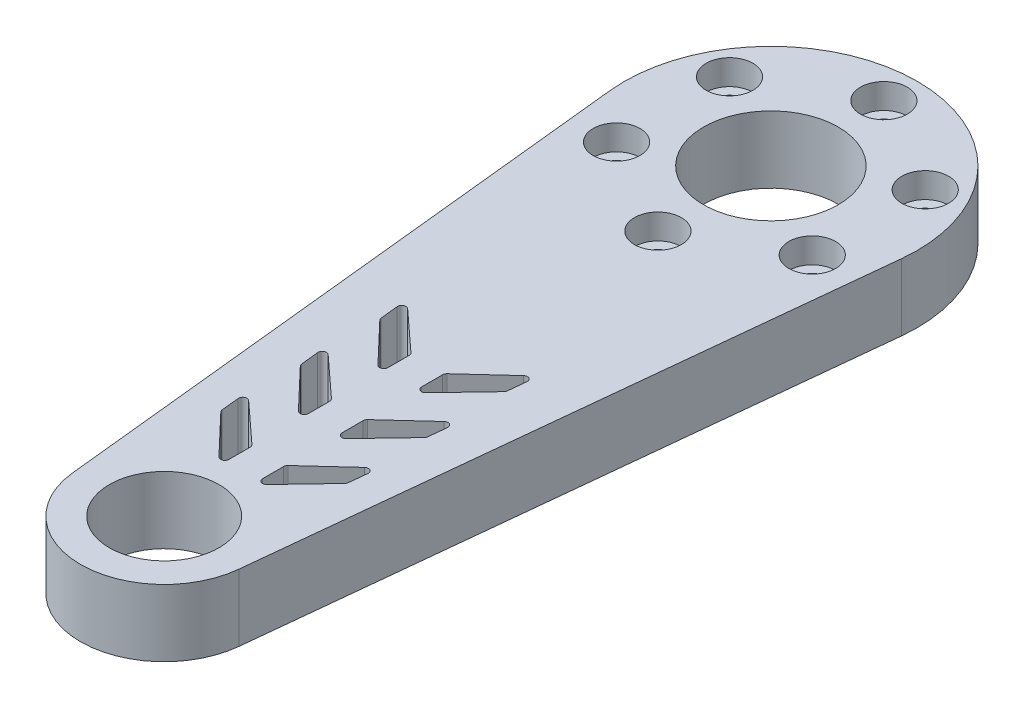
SolidWorks part; units mm, degrees
material "Thornel Mat VMA"
ref_plane "前视基准面" through (0, 0, 0) normal (0, 0, 1) x (1, 0, 0)
ref_plane "上视基准面" through (0, 0, 0) normal (0, 1, 0) x (1, 0, 0)
ref_plane "右视基准面" through (0, 0, 0) normal (1, 0, 0) x (0, 0, -1)
ref_plane "基准面4" through (0, 4, 0) normal (0, 1, 0) x (1, 0, 0)
sketch "草图1" plane through (0, 4, 0) normal (0, 1, 0) x (1, 0, 0)
  line L0 (-17.4061, -1.8103) -> (-9.9463, -73.5345)
  line L1 (9.9463, -73.5345) -> (17.4061, -1.8103)
  arc A0 (-9.9463, -73.5345) -> (9.9463, -73.5345) centre (0, -72.5) ccw
  arc A1 (17.4061, -1.8103) -> (-17.4061, -1.8103) centre (0, 0) ccw
extrude "凸台-拉伸1" add sketch "草图1" against normal blind 8
sketch "草图2" plane through (0, 4, 0) normal (0, 1, 0) x (-1, 0, 0)
  line L0 (2, 43.7505) -> (2, 41)
  line L1 (2, 41) -> (6.9232, 36.4832)
  line L2 (7.7585, 36.9034) -> (7.5188, 39.2084)
  line L3 (7.5188, 39.2084) -> (2.862, 44.0954)
  arc A0 (2.862, 44.0954) -> (2, 43.7505) centre (2.5, 43.7505) ccw
  arc A1 (6.9232, 36.4832) -> (7.7585, 36.9034) centre (7.2612, 36.8517) ccw
extrude "切除-拉伸1" cut sketch "草图2" against normal through all
sketch "草图3" plane through (0, 4, 0) normal (0, 1, 0) x (-1, 0, 0)
  line L0 (-6.9232, 36.4832) -> (-2, 41)
  line L1 (-2, 41) -> (-2, 43.7505)
  line L2 (-2.862, 44.0954) -> (-7.5188, 39.2084)
  line L3 (-7.5188, 39.2084) -> (-7.7585, 36.9034)
  arc A0 (-2, 43.7505) -> (-2.862, 44.0954) centre (-2.5, 43.7505) ccw
  arc A1 (-7.7585, 36.9034) -> (-6.9232, 36.4832) centre (-7.2612, 36.8517) ccw
extrude "切除-拉伸2" cut sketch "草图3" against normal through all
sketch "草图4" plane through (0, 4, 0) normal (0, 1, 0) x (-1, 0, 0)
  line L0 (2, 53.2505) -> (2, 50.5)
  line L1 (2, 50.5) -> (6.9232, 45.9832)
  line L2 (7.7585, 46.4034) -> (7.5188, 48.7084)
  line L3 (7.5188, 48.7084) -> (2.862, 53.5954)
  arc A0 (2.862, 53.5954) -> (2, 53.2505) centre (2.5, 53.2505) ccw
  arc A1 (6.9232, 45.9832) -> (7.7585, 46.4034) centre (7.2612, 46.3517) ccw
extrude "切除-拉伸3" cut sketch "草图4" against normal through all
sketch "草图5" plane through (0, 4, 0) normal (0, 1, 0) x (-1, 0, 0)
  line L0 (-6.9232, 45.9832) -> (-2, 50.5)
  line L1 (-2, 50.5) -> (-2, 53.2505)
  line L2 (-2.862, 53.5954) -> (-7.5188, 48.7084)
  line L3 (-7.5188, 48.7084) -> (-7.7585, 46.4034)
  arc A0 (-2, 53.2505) -> (-2.862, 53.5954) centre (-2.5, 53.2505) ccw
  arc A1 (-7.7585, 46.4034) -> (-6.9232, 45.9832) centre (-7.2612, 46.3517) ccw
extrude "切除-拉伸4" cut sketch "草图5" against normal through all
sketch "草图6" plane through (0, 4, 0) normal (0, 1, 0) x (-1, 0, 0)
  line L0 (2, 62.7505) -> (2, 60)
  line L1 (2, 60) -> (6.9232, 55.4832)
  line L2 (7.7585, 55.9034) -> (7.5188, 58.2084)
  line L3 (7.5188, 58.2084) -> (2.862, 63.0954)
  arc A0 (2.862, 63.0954) -> (2, 62.7505) centre (2.5, 62.7505) ccw
  arc A1 (6.9232, 55.4832) -> (7.7585, 55.9034) centre (7.2612, 55.8517) ccw
extrude "切除-拉伸5" cut sketch "草图6" against normal through all
sketch "草图7" plane through (0, -4, 0) normal (0, -1, 0) x (1, 0, 0)
  line L0 (2, 62.7505) -> (2, 60)
  line L1 (2, 60) -> (6.9232, 55.4832)
  line L2 (7.7585, 55.9034) -> (7.5188, 58.2084)
  line L3 (7.5188, 58.2084) -> (2.862, 63.0954)
  arc A0 (6.9232, 55.4832) -> (7.7585, 55.9034) centre (7.2612, 55.8517) ccw
  arc A1 (2.862, 63.0954) -> (2, 62.7505) centre (2.5, 62.7505) ccw
extrude "切除-拉伸6" cut sketch "草图7" against normal through all
hole_wizard "Ø16.0 (16) 直径孔1" positions "草图15" profile "草图14" hole size "Ø16.0" standard "ANSI Metric"
sketch "草图15" plane through (0, -4, 0) normal (0, -1, 0) x (-1, 0, 0)
  point P0 (0, 0)
sketch "草图14" plane through (0, -4, 0) normal (1, 0, 0) x (0, 0, -1)
  line L0 (0, 0) -> (0, 8)
  line L1 (0, 8) -> (8.05, 8)
  line L2 (8.05, 8) -> (8.05, 0)
  line L5 (8.05, 0) -> (0, 0)
  line L11 (0, -6.35) -> (0, 107.95) construction
  dimension "通孔孔直径" = 16.1
  dimension "通孔孔深度" = 8
hole_wizard "Ø13.0 (13) 直径孔1" positions "草图17" profile "草图16" hole size "Ø13.0" standard "ANSI Metric"
sketch "草图17" plane through (0, 4, 0) normal (0, 1, 0) x (1, 0, 0)
  point P0 (0, -72.5)
sketch "草图16" plane through (0, 4, 72.5) normal (1, 0, 0) x (0, 0, 1)
  line L0 (0, 0) -> (0, 8)
  line L1 (0, 8) -> (6.55, 8)
  line L2 (6.55, 8) -> (6.55, 0)
  line L5 (6.55, 0) -> (0, 0)
  line L11 (0, -6.35) -> (0, 107.95) construction
  dimension "通孔孔直径" = 13.1
  dimension "通孔孔深度" = 8
hole_wizard "M2.5 六角头机械螺钉的柱形沉头孔1" positions "草图19" profile "草图18" counterbore size "M2.5" standard "ANSI Metric"
sketch "草图19" plane through (0, 4, 0) normal (0, 1, 0) x (1, 0, 0)
  point P0 (-11.6913, -6.75)
  point P1 (-11.6913, 6.75)
  point P2 (0, 13.5)
  point P3 (11.6913, 6.75)
  point P4 (11.6913, -6.75)
  point P5 (0, -13.5)
sketch "草图18" plane through (-11.6913, 4, 6.75) normal (1, 0, 0) x (0, 0, 1)
  line L0 (0, 0) -> (0, 8)
  line L1 (0, 8) -> (1.55, 8)
  line L3 (1.55, 8) -> (1.55, 3)
  line L4 (1.55, 3) -> (2.8, 3)
  line L5 (2.8, 3) -> (2.8, 0)
  line L7 (2.8, 0) -> (0, 0)
  line L11 (0, -6.35) -> (0, 107.95) construction
  dimension "通孔孔直径" = 3.1
  dimension "通孔孔深度" = 8
  dimension "柱形沉头孔直径" = 5.6
  dimension "柱形沉头孔深度" = 3
fillet "圆角1" radius 0.5 12 edges at (2, 0, 50.5) (2, 0, 60) (-2, 0, 60) (-2, 0, 41) (7.5188, 0, 48.7084) (7.5188, 0, 39.2084) (-7.5188, 0, 58.2084) (2, 0, 41) (7.5188, 0, 58.2084) (-7.5188, 0, 48.7084) (-2, 0, 50.5) (-7.5188, 0, 39.2084)
